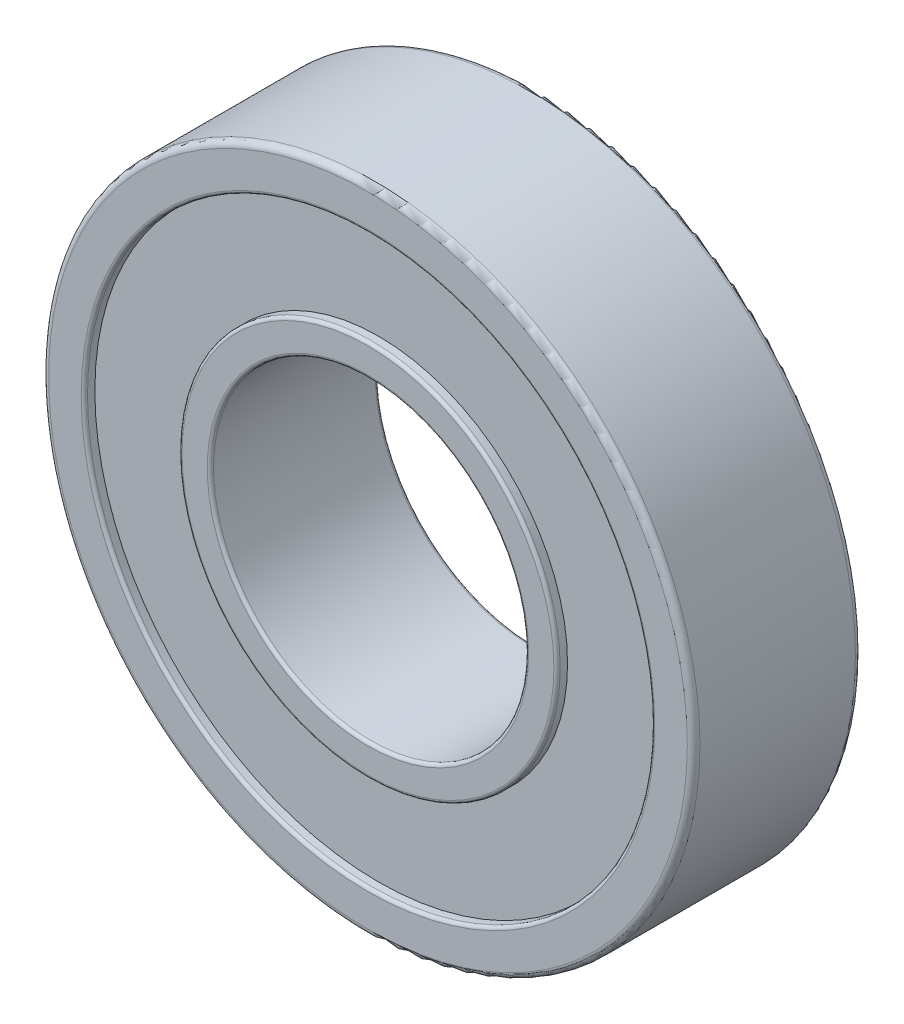
SolidWorks part; units mm, degrees
ref_plane "Ön Düzlem" through (0, 0, 0) normal (0, 0, 1) x (1, 0, 0)
ref_plane "Üst Düzlem" through (0, 0, 0) normal (0, 1, 0) x (1, 0, 0)
ref_plane "Sağ Düzlem" through (0, 0, 0) normal (1, 0, 0) x (0, 0, -1)
sketch "Çizim1" plane through (0, 0, 0) normal (0, 0, 1) x (1, 0, 0)
  circle A0 centre (0, 0) radius 15
  circle A1 centre (0, 0) radius 31
  dimension "D1" = 30
  dimension "D2" = 62
extrude "Yükseklik-Ekstrüzyon1" add sketch "Çizim1" along normal blind 16
sketch "Çizim2" plane through (0, 0, 0) normal (0, 0, -1) x (-1, 0, 0)
  circle A0 centre (0, 0) radius 18
  circle A1 centre (0, 0) radius 27
  dimension "D1" = 36
  dimension "D2" = 54
extrude "Kes-Ekstrüzyon1" cut sketch "Çizim2" against normal blind 1
sketch "Çizim3" plane through (0, 0, 16) normal (0, 0, 1) x (1, 0, 0)
  circle A0 centre (0, 0) radius 18
  circle A1 centre (0, 0) radius 27
  dimension "D1" = 36
  dimension "D2" = 54
extrude "Kes-Ekstrüzyon2" cut sketch "Çizim3" against normal blind 1
fillet "Radyus1" radius 0.6 2 edges at (31, 0, 16) (31, 0, 0)
fillet "Radyus2" radius 0.3 6 edges at (15, 0, 16) (18, 0, 16) (27, 0, 16) (15, 0, 0) (-18, 0, 0) (-27, 0, 0)
